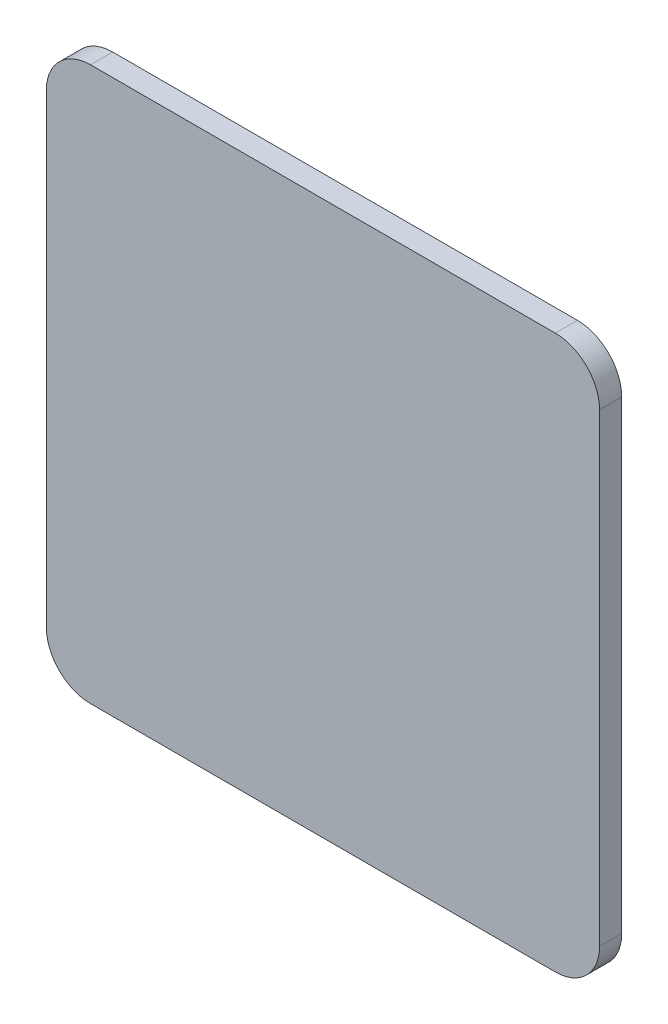
SolidWorks part; units mm, degrees
ref_plane "Front Plane" through (0, 0, 0) normal (0, 0, 1) x (1, 0, 0)
ref_plane "Top Plane" through (0, 0, 0) normal (0, 1, 0) x (1, 0, 0)
ref_plane "Right Plane" through (0, 0, 0) normal (1, 0, 0) x (0, 0, -1)
sketch "Sketch1" plane through (0, 0, 0) normal (0, 0, 1) x (1, 0, 0)
  line L0 (53.34, 58.42) -> (-53.34, 58.42)
  line L1 (53.34, 63.5) -> (-53.34, 63.5)
  line L2 (63.5, 53.34) -> (63.5, -53.34)
  line L3 (53.34, -63.5) -> (-53.34, -63.5)
  line L4 (-63.5, 53.34) -> (-63.5, -53.34)
  line L5 (63.5, 63.5) -> (-63.5, -63.5) construction
  line L6 (63.5, -63.5) -> (-63.5, 63.5) construction
  line L7 (-58.42, 53.34) -> (-58.42, -53.34)
  line L8 (53.34, -58.42) -> (-53.34, -58.42)
  line L9 (58.42, 53.34) -> (58.42, -53.34)
  arc A0 (63.5, 53.34) -> (53.34, 63.5) centre (53.34, 53.34) ccw
  arc A1 (53.34, -63.5) -> (63.5, -53.34) centre (53.34, -53.34) ccw
  arc A2 (-63.5, -53.34) -> (-53.34, -63.5) centre (-53.34, -53.34) ccw
  arc A3 (-53.34, 63.5) -> (-63.5, 53.34) centre (-53.34, 53.34) ccw
  arc A4 (-53.34, 58.42) -> (-58.42, 53.34) centre (-53.34, 53.34) ccw
  arc A5 (-58.42, -53.34) -> (-53.34, -58.42) centre (-53.34, -53.34) ccw
  arc A6 (53.34, -58.42) -> (58.42, -53.34) centre (53.34, -53.34) ccw
  arc A7 (58.42, 53.34) -> (53.34, 58.42) centre (53.34, 53.34) ccw
  point P0 (0, 0)
  dimension "D3" = 10.16
  dimension "D1" = 127
  dimension "D2" = 127
  dimension "D4" = 5.08
extrude "Boss-Extrude1" add sketch "Sketch1" along normal blind 5.08 contours L9 A7 L0 A4 L7 A5 L8 A6 | L1 A3 L4 A2 L3 A1 L2 A0 A7 L9 A6 L8 A5 L7 A4 L0
